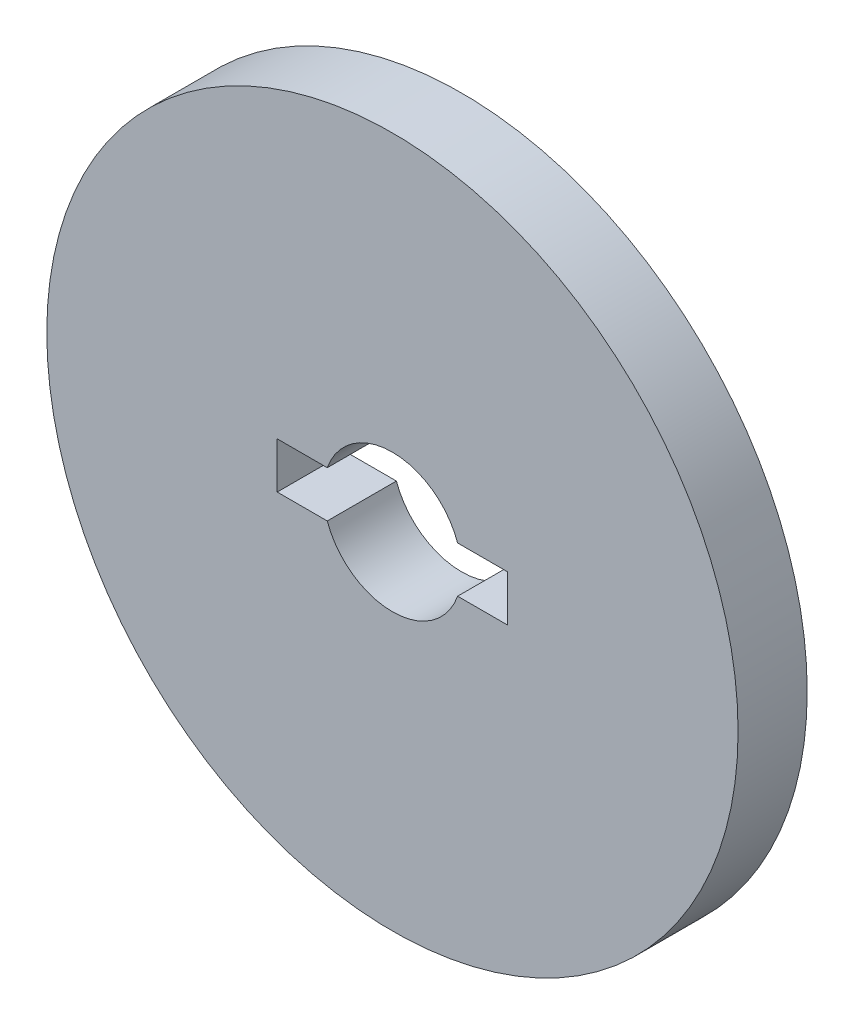
SolidWorks part; units mm, degrees
ref_plane "Front" through (0, 0, 0) normal (0, 0, 1) x (1, 0, 0)
ref_plane "Top" through (0, 0, 0) normal (0, 1, 0) x (1, 0, 0)
ref_plane "Right" through (0, 0, 0) normal (1, 0, 0) x (0, 0, -1)
sketch "Sketch1" plane through (0, 0, 0) normal (0, 0, 1) x (1, 0, 0)
  line L0 (-50, 10) -> (50, 10)
  line L1 (-50, 10) -> (-50, -10)
  line L2 (-50, -10) -> (50, -10)
  line L3 (50, 10) -> (50, -10)
  circle A0 centre (0, 0) radius 30
  circle A1 centre (0, 0) radius 150
extrude "Boss-Extrude1" add sketch "Sketch1" along normal blind 30 contours A1 A0 L0 L3 L2 L1
